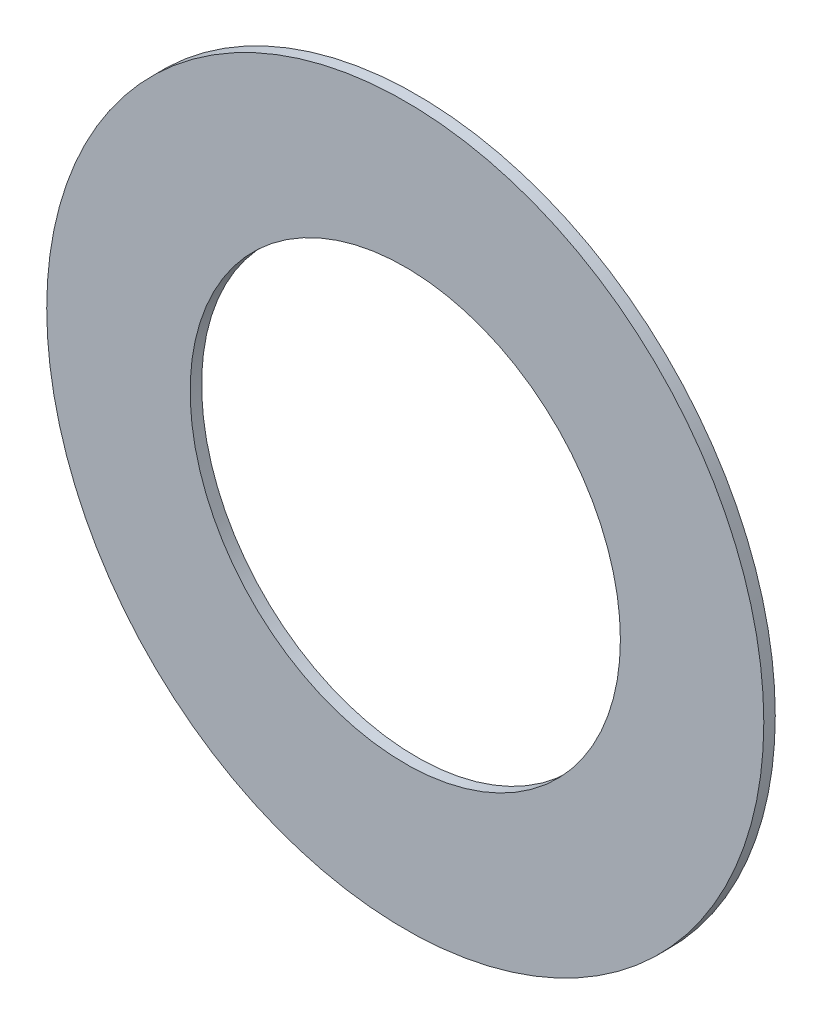
SolidWorks part; units mm, degrees
material "AISI 1020"
ref_plane "Front Plane" through (0, 0, 0) normal (0, 0, 1) x (1, 0, 0)
ref_plane "Top Plane" through (0, 0, 0) normal (0, 1, 0) x (1, 0, 0)
ref_plane "Right Plane" through (0, 0, 0) normal (1, 0, 0) x (0, 0, -1)
sketch "Sketch1" plane through (0, 0, 0) normal (0, 0, 1) x (1, 0, 0)
  circle A0 centre (0, 0) radius 4.7625
  circle A1 centre (0, 0) radius 7.9375
  dimension "D1" = 9.525
  dimension "D2" = 15.875
extrude "Boss-Extrude1" add sketch "Sketch1" along normal blind 0.254
